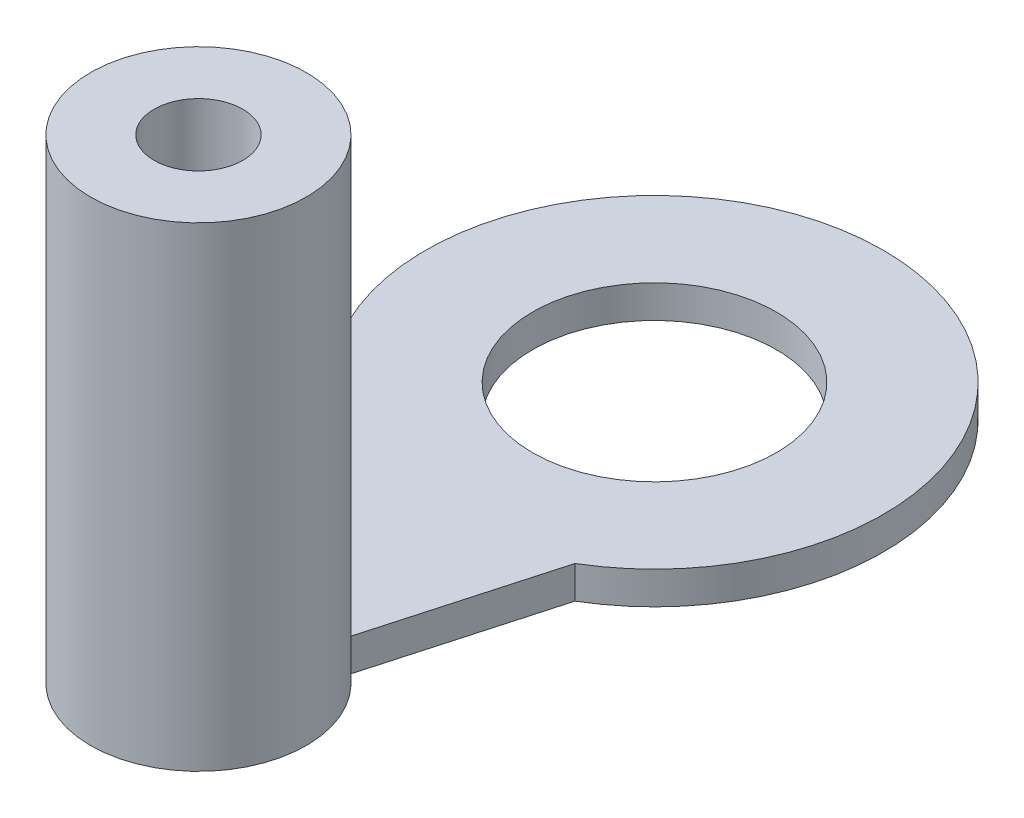
SolidWorks part; units mm, degrees
ref_plane "Front Plane" through (0, 0, 0) normal (0, 0, 1) x (1, 0, 0)
ref_plane "Top Plane" through (0, 0, 0) normal (0, 1, 0) x (1, 0, 0)
ref_plane "Right Plane" through (0, 0, 0) normal (1, 0, 0) x (0, 0, -1)
sketch "Sketch1" plane through (0, 0, 0) normal (0, 1, 0) x (1, 0, 0)
  circle A0 centre (0, 0) radius 5.96
extrude "Boss-Extrude1" add sketch "Sketch1" along normal blind 0.85
hole_wizard "1/4 (0.25) Diameter Hole1" positions "Sketch2" profile "Sketch3" hole size "1/4" standard "ANSI Inch" end condition up to next
sketch "Sketch2" plane through (0, 0.85, 0) normal (0, 1, 0) x (1, 0, 0)
  point P0 (0, 0)
sketch "Sketch3" plane through (0, 0.85, 0) normal (1, 0, 0) x (0, 0, 1)
  line L0 (0, 0) -> (0, 0.85)
  line L1 (0, 0.85) -> (3.175, 0.85)
  line L2 (3.175, 0.85) -> (3.175, 0)
  line L5 (3.175, 0) -> (0, 0)
  line L11 (0, -6.35) -> (0, 107.95) construction
  dimension "Thru Hole Dia." = 6.35
  dimension "Thru Hole Depth" = 0.85
sketch "Sketch4" plane through (0, 0.85, 0) normal (0, 1, 0) x (1, 0, 0)
  line L0 (0, -3.175) -> (0, -11.875)
  circle A0 centre (0, 0) radius 3.175 construction
sketch "Sketch5" plane through (0, 0.85, 0) normal (0, 1, 0) x (1, 0, 0)
  circle A0 centre (0, -11.875) radius 1.155
  circle A1 centre (0, -11.875) radius 2.81
extrude "Boss-Extrude2" add sketch "Sketch5" along normal blind 11.52 and the other way blind 0.85 separate body
sketch "Sketch6" plane through (0, 0.85, 0) normal (0, 1, 0) x (1, 0, 0)
  line L0 (-1.155, -11.875) -> (-3.037, -5.1282)
  line L1 (1.155, -11.875) -> (3.0499, -5.1205)
  line L2 (-3.037, -5.1282) -> (3.0499, -5.1205)
  line L3 (1.155, -11.875) -> (-1.155, -11.875)
  circle A0 centre (0, -11.875) radius 1.155 construction
  circle A1 centre (0, 0) radius 5.96 construction
extrude "Boss-Extrude3" add sketch "Sketch6" against normal up to surface (0.85 mm away) up to face at (0, 0, 3.175)
sketch "Sketch9" plane through (0, 0.85, 0) normal (0, 1, 0) x (1, 0, 0)
  circle A0 centre (0, -11.875) radius 1.155
extrude "Cut-Extrude1" cut sketch "Sketch9" against normal through all
sketch "Sketch10" plane through (0, 0, 0) normal (0, -1, 0) x (-1, 0, 0)
  line L0 (0, -11.875) -> (0, 0)
